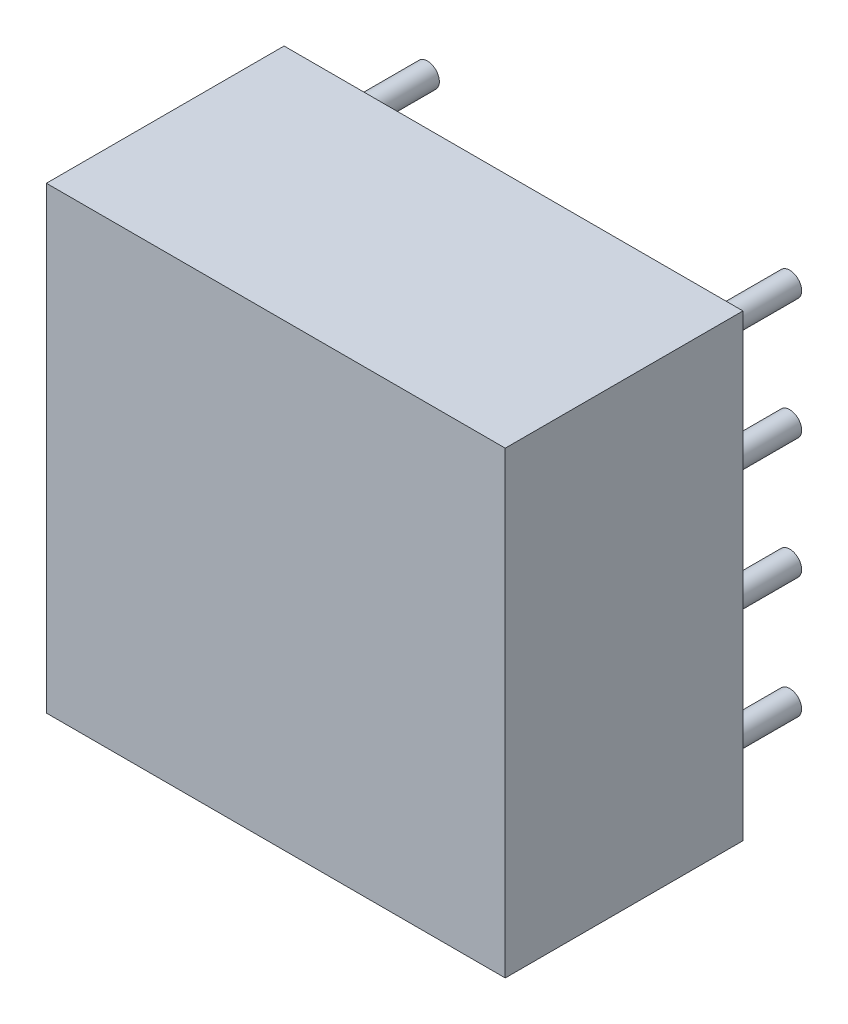
SolidWorks part; units mm, degrees
ref_plane "Front Plane" through (0, 0, 0) normal (0, 0, 1) x (1, 0, 0)
ref_plane "Top Plane" through (0, 0, 0) normal (0, 1, 0) x (1, 0, 0)
ref_plane "Right Plane" through (0, 0, 0) normal (1, 0, 0) x (0, 0, -1)
sketch "Sketch1" plane through (0, 0, 0) normal (0, 0, 1) x (1, 0, 0)
  line L0 (-1.016, -1.016) -> (8.636, -1.016)
  line L1 (8.636, -1.016) -> (8.636, 8.636)
  line L2 (8.636, 8.636) -> (-1.016, 8.636)
  line L3 (-1.016, 8.636) -> (-1.016, -1.016)
extrude "Component_Outline" add sketch "Sketch1" along normal blind 5 separate body
sketch "Sketch2" plane through (0, 0, 0) normal (0, 0, 1) x (1, 0, 0)
  circle A0 centre (0, 0) radius 0.25
extrude "1" add sketch "Sketch2" against normal blind 2 separate body
sketch "Sketch3" plane through (0, 0, 0) normal (0, 0, 1) x (1, 0, 0)
  circle A0 centre (0, 2.54) radius 0.25
extrude "2" add sketch "Sketch3" against normal blind 2 separate body
sketch "Sketch4" plane through (0, 0, 0) normal (0, 0, 1) x (1, 0, 0)
  circle A0 centre (0, 5.08) radius 0.25
extrude "3" add sketch "Sketch4" against normal blind 2 separate body
sketch "Sketch5" plane through (0, 0, 0) normal (0, 0, 1) x (1, 0, 0)
  circle A0 centre (0, 7.62) radius 0.25
extrude "4" add sketch "Sketch5" against normal blind 2 separate body
sketch "Sketch6" plane through (0, 0, 0) normal (0, 0, 1) x (1, 0, 0)
  circle A0 centre (7.62, 0) radius 0.25
extrude "5" add sketch "Sketch6" against normal blind 2 separate body
sketch "Sketch7" plane through (0, 0, 0) normal (0, 0, 1) x (1, 0, 0)
  circle A0 centre (7.62, 2.54) radius 0.25
extrude "6" add sketch "Sketch7" against normal blind 2 separate body
sketch "Sketch8" plane through (0, 0, 0) normal (0, 0, 1) x (1, 0, 0)
  circle A0 centre (7.62, 5.08) radius 0.25
extrude "7" add sketch "Sketch8" against normal blind 2 separate body
sketch "Sketch9" plane through (0, 0, 0) normal (0, 0, 1) x (1, 0, 0)
  circle A0 centre (7.62, 7.62) radius 0.25
extrude "8" add sketch "Sketch9" against normal blind 2 separate body
sketch3d "3DSketch1"
  line L0 (0, 0, 0) -> (1, 0, 0)
  line L1 (0, 0, 0) -> (0, 1, 0)
  line L2 (0, 0, 0) -> (0, 0, 1)
  point P0 (0, 0, 0)
